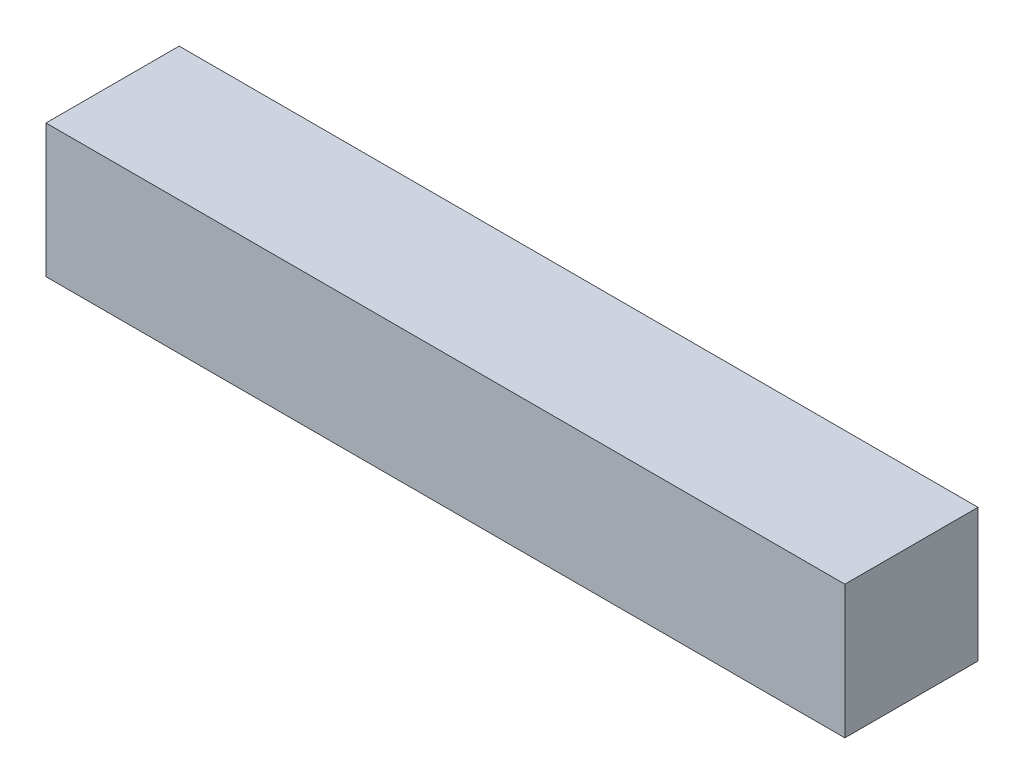
SolidWorks part; units mm, degrees
ref_plane "Front Plane" through (0, 0, 0) normal (0, 0, 1) x (1, 0, 0)
ref_plane "Top Plane" through (0, 0, 0) normal (0, 1, 0) x (1, 0, 0)
ref_plane "Right Plane" through (0, 0, 0) normal (1, 0, 0) x (0, 0, -1)
sketch "Sketch1" plane through (0, 0, 0) normal (1, 0, 0) x (0, 0, -1)
  line L1 (0, 0) -> (-25.4, 0)
  line L2 (0, 0) -> (0, 25.4)
  line L3 (0, 25.4) -> (-25.4, 25.4)
  line L4 (-25.4, 0) -> (-25.4, 25.4)
  dimension "D1" = 25.4
  dimension "D2" = 25.4
extrude "Boss-Extrude1" add sketch "Sketch1" along normal blind 152.4
